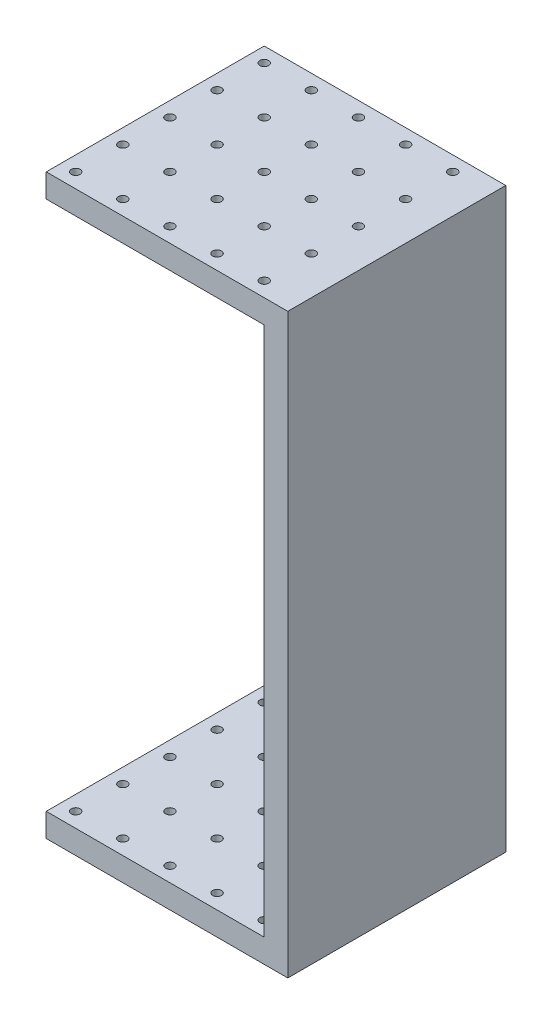
SolidWorks part; units mm, degrees
ref_plane "Front Plane" through (0, 0, 0) normal (0, 0, 1) x (1, 0, 0)
ref_plane "Top Plane" through (0, 0, 0) normal (0, 1, 0) x (1, 0, 0)
ref_plane "Right Plane" through (0, 0, 0) normal (1, 0, 0) x (0, 0, -1)
sketch "Sketch1" plane through (0, 0, 0) normal (0, 1, 0) x (1, 0, 0)
  line L1 (10.25, -9.25) -> (-10.25, -9.25)
  line L2 (10.25, -9.25) -> (10.25, 9.25)
  line L3 (10.25, 9.25) -> (-10.25, 9.25)
  line L4 (-10.25, -9.25) -> (-10.25, 9.25)
  line L5 (10.25, -9.25) -> (-10.25, 9.25) construction
  line L6 (10.25, 9.25) -> (-10.25, -9.25) construction
  point P0 (0, 0)
  dimension "D1" = 20.5
  dimension "D2" = 18.5
extrude "Boss-Extrude1" add sketch "Sketch1" along normal blind 2
sketch "Sketch2" plane through (0, 2, 0) normal (0, 1, 0) x (1, 0, 0)
  line L0 (-10.25, 9.25) -> (10.25, -9.25) construction
  line L1 (10.25, 9.25) -> (-10.25, -9.25) construction
  line L3 (10.25, 9.25) -> (-10.25, 9.25) construction
  line L5 (10.25, -9.25) -> (8.25, -9.25)
  line L7 (8.25, -9.25) -> (8.25, 9.25)
  line L8 (8.25, 9.25) -> (10.25, 9.25)
  line L9 (-10.25, -9.25) -> (10.25, -9.25) construction
  line L12 (10.25, 9.25) -> (10.25, -9.25)
  dimension "D2" = 2
extrude "Boss-Extrude2" add sketch "Sketch2" along normal blind 45
sketch "Sketch3" plane through (0, 0, 0) normal (0, -1, 0) x (1, 0, 0)
  line L0 (-9, 8) -> (-9, 9.25) construction
  line L1 (10.25, 9.25) -> (-10.25, -9.25) construction
  line L2 (-10.25, -9.25) -> (-10.25, 9.25) construction
  line L7 (-10.25, 9.25) -> (10.25, 9.25) construction
  circle A0 centre (-9, 8) radius 0.375
  circle A1 centre (-5, 8) radius 0.375
  circle A2 centre (-1, 8) radius 0.375
  circle A3 centre (3, 8) radius 0.375
  circle A4 centre (7, 8) radius 0.375
  circle A9 centre (-5, 4) radius 0.375
  circle A10 centre (-1, 4) radius 0.375
  circle A11 centre (3, 4) radius 0.375
  circle A12 centre (7, 4) radius 0.375
  circle A17 centre (-5, 0) radius 0.375
  circle A18 centre (-1, 0) radius 0.375
  circle A19 centre (3, 0) radius 0.375
  circle A20 centre (7, 0) radius 0.375
  circle A25 centre (-5, -4) radius 0.375
  circle A26 centre (-1, -4) radius 0.375
  circle A27 centre (3, -4) radius 0.375
  circle A28 centre (7, -4) radius 0.375
  circle A33 centre (-5, -8) radius 0.375
  circle A34 centre (-1, -8) radius 0.375
  circle A35 centre (3, -8) radius 0.375
  circle A36 centre (7, -8) radius 0.375
  circle A41 centre (-5, -12) radius 0.375
  circle A42 centre (-1, -12) radius 0.375
  circle A43 centre (3, -12) radius 0.375
  circle A44 centre (7, -12) radius 0.375
  circle A73 centre (-9, 4) radius 0.375
  circle A74 centre (-9, 0) radius 0.375
  circle A75 centre (-9, -4) radius 0.375
  circle A76 centre (-9, -8) radius 0.375
  circle A77 centre (-9, -12) radius 0.375
  dimension "D1" = 0.75
  dimension "D2" = 6
  dimension "D3" = 1.25
  dimension "D4" = 1.25
  dimension "D5" = 5
sketch "Sketch4" plane through (0, 47, 0) normal (0, 1, 0) x (1, 0, 0)
  line L1 (-10.25, 9.25) -> (10.25, 9.25)
  line L2 (-10.25, 9.25) -> (-10.25, -9.25)
  line L3 (-10.25, -9.25) -> (10.25, -9.25)
  line L4 (10.25, 9.25) -> (10.25, -9.25)
  line L5 (-10.25, 9.25) -> (10.25, -9.25) construction
  line L6 (-10.25, -9.25) -> (10.25, 9.25) construction
  point P0 (0, 0)
  dimension "D1" = 20.5
  dimension "D2" = 18.5
extrude "Boss-Extrude3" add sketch "Sketch4" along normal blind 2
extrude "Cut-Extrude1" cut sketch "Sketch3" against normal through all
